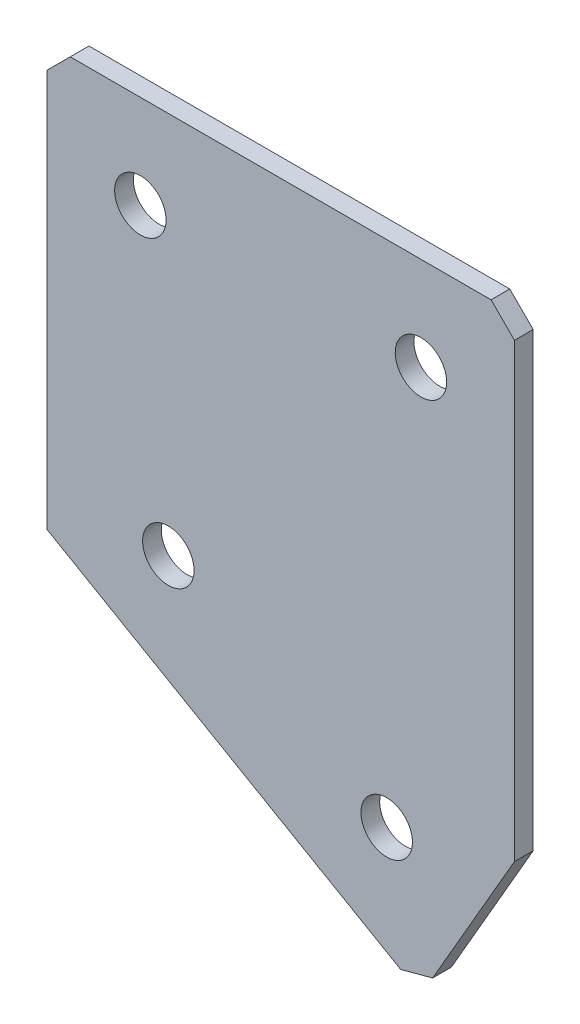
SolidWorks part; units mm, degrees
material "Простая углеродистая сталь"
ref_plane "Спереди" through (0, 0, 0) normal (0, 0, 1) x (1, 0, 0)
ref_plane "Сверху" through (0, 0, 0) normal (0, 1, 0) x (1, 0, 0)
ref_plane "Справа" through (0, 0, 0) normal (1, 0, 0) x (0, 0, -1)
sketch "Эскиз3" plane through (0, 0, 0) normal (0, 0, -1) x (1, 0, 0)
  line L0 (0, 0) -> (50, 0)
  line L1 (50, 0) -> (50, 50.7735)
  line L2 (0, 0) -> (0, 45)
  line L3 (0, 45) -> (40, 68.094)
  line L4 (40, 68.094) -> (50, 50.7735)
  dimension "D1" = 50
  dimension "D2" = 45
  dimension "D3" = 20
  dimension "D4" = 30
  dimension "D5" = 50.7735
extrude "Бобышка-Вытянуть1" add sketch "Эскиз3" along normal blind 2
hole_wizard "Отверстие с зазором M51" positions "Эскиз4" profile "Эскиз5" hole size "M5" standard "DIN" end condition through all
sketch "Эскиз4" plane through (0, 0, -2) normal (0, 0, -1) x (1, 0, 0)
  line L0 (12.9904, 40.953) -> (36.3397, 54.4338) construction
  line L2 (40, 68.094) -> (0, 45) construction
  line L3 (10, 10) -> (40, 10) construction
  line L5 (0, 0) -> (50, 0) construction
  line L6 (0, 45) -> (0, 0) construction
  line L7 (50, 0) -> (50, 50.7735) construction
  line L8 (50, 50.7735) -> (40, 68.094) construction
  line L9 (12.9904, 40.953) -> (0, 33.453) construction
  point P0 (10, 10)
  point P2 (40, 10)
  point P4 (12.9904, 40.953)
  point P6 (36.3397, 54.4338)
  dimension "D1" = 10
  dimension "D2" = 10
  dimension "D3" = 10
  dimension "D4" = 10
  dimension "D5" = 10
  dimension "D6" = 15
  dimension "D7" = 26.9615
  dimension "D8" = 30
sketch "Эскиз5" plane through (10, -10, -2) normal (1, 0, 0) x (0, 1, 0)
  line L0 (0, 0) -> (0, 2)
  line L1 (0, 2) -> (2.75, 2)
  line L2 (2.75, 2) -> (2.75, 0)
  line L5 (2.75, 0) -> (0, 0)
  line L11 (0, -6.35) -> (0, 107.95) construction
  dimension "Диаметр сквозного отверстия" = 5.5
  dimension "Глубина сквозного отверстия" = 2
chamfer "Фаска1" distance 2.5 distance2 2.5 3 edges at (40, -68.094, -1) (50, 0, -1) (0, 0, -1)
